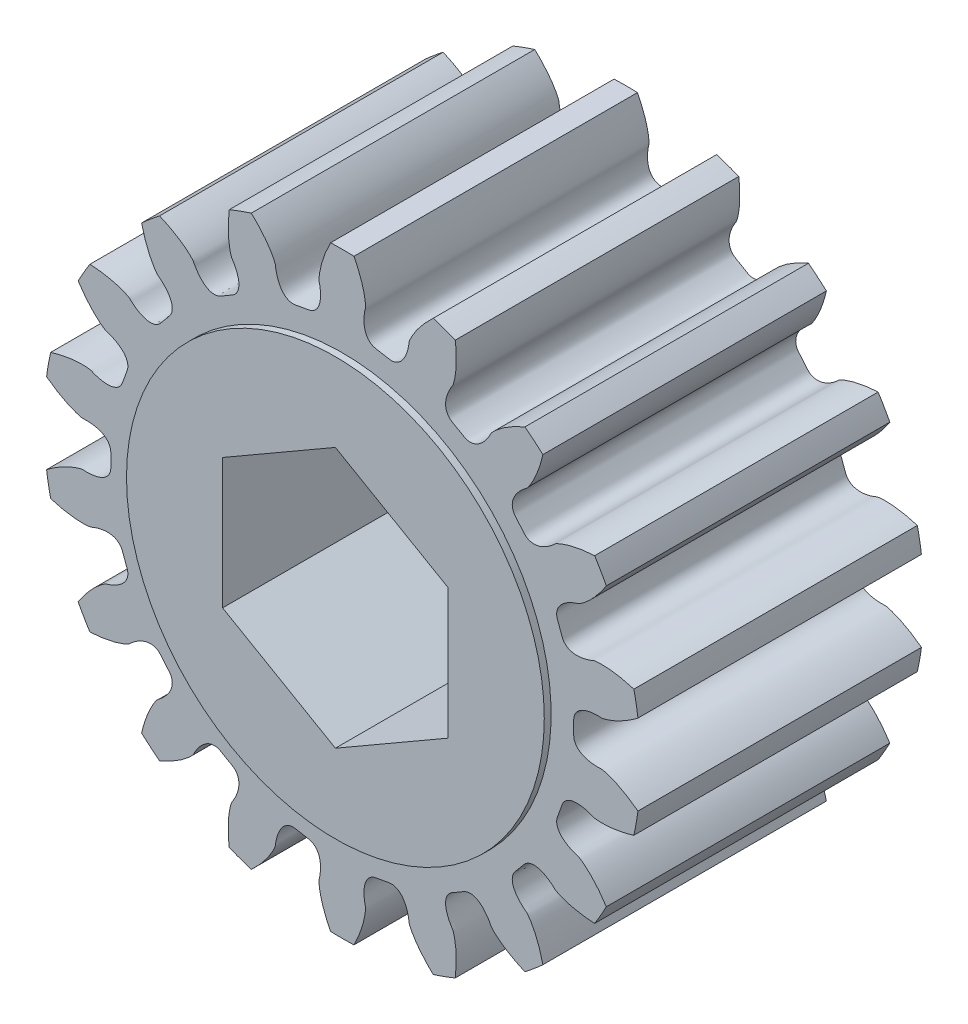
SolidWorks part; units mm, degrees
material "7075-T6 (SN)"
ref_plane "Front Plane" through (0, 0, 0) normal (0, 0, 1) x (1, 0, 0)
ref_plane "Top Plane" through (0, 0, 0) normal (0, 1, 0) x (1, 0, 0)
ref_plane "Right Plane" through (0, 0, 0) normal (1, 0, 0) x (0, 0, -1)
ref_plane "Plane1" through (0, 0, 6.0325) normal (0, 0, 1) x (1, 0, 0)
sketch "Sketch1" plane through (0, 0, 6.0325) normal (0, 0, 1) x (1, 0, 0)
  arc A0 (12.411, -2.694) -> (12.5839, -1.7132) centre (0, 0) ccw
  arc A1 (12.5839, 1.7132) -> (12.411, 2.694) centre (0, 0) ccw
  arc A2 (11.239, 5.9139) -> (10.7411, 6.7764) centre (0, 0) ccw
  arc A3 (8.5386, 9.4012) -> (7.7757, 10.0414) centre (0, 0) ccw
  arc A4 (4.8082, 11.7546) -> (3.8724, 12.0952) centre (0, 0) ccw
  arc A5 (0.498, 12.6902) -> (-0.498, 12.6902) centre (0, 0) ccw
  arc A6 (-3.8724, 12.0952) -> (-4.8082, 11.7546) centre (0, 0) ccw
  arc A7 (-7.7757, 10.0414) -> (-8.5386, 9.4012) centre (0, 0) ccw
  arc A8 (-10.7411, 6.7764) -> (-11.239, 5.9139) centre (0, 0) ccw
  arc A9 (-12.411, 2.694) -> (-12.5839, 1.7132) centre (0, 0) ccw
  arc A10 (-12.5839, -1.7132) -> (-12.411, -2.694) centre (0, 0) ccw
  arc A11 (-11.239, -5.9139) -> (-10.7411, -6.7764) centre (0, 0) ccw
  arc A12 (-8.5386, -9.4012) -> (-7.7757, -10.0414) centre (0, 0) ccw
  arc A13 (-4.8082, -11.7546) -> (-3.8724, -12.0952) centre (0, 0) ccw
  arc A14 (-0.498, -12.6902) -> (0.498, -12.6902) centre (0, 0) ccw
  arc A15 (3.8724, -12.0952) -> (4.8082, -11.7546) centre (0, 0) ccw
  arc A16 (7.7757, -10.0414) -> (8.5386, -9.4012) centre (0, 0) ccw
  arc A17 (10.7411, -6.7764) -> (11.239, -5.9139) centre (0, 0) ccw
  spline S0 degree 3 poles (11.239, -5.9139) (11.1509, -5.7775) (11.0298, -5.6051) (10.8706, -5.4047) (10.783, -5.3007) (10.6983, -5.2057) (10.6171, -5.1195) (10.5396, -5.0419) (10.4664, -4.9725) (10.3977, -4.911) (10.3341, -4.8571) (10.2759, -4.8106) (10.2233, -4.771) (10.1769, -4.7378) (10.1275, -4.7053) (10.0518, -4.6541) (9.95, -4.6355) (9.8549, -4.5968) (9.7835, -4.5675) (9.7159, -4.5362) (9.6517, -4.5038) (9.5908, -4.4699) (9.5333, -4.4347) (9.479, -4.3981) (9.4279, -4.3599) (9.3799, -4.3199) (9.3348, -4.2779) (9.2928, -4.2333) (9.2539, -4.1857) (9.2182, -4.1342) (9.1862, -4.078) (9.1588, -4.016) (9.1377, -3.9474) (9.125, -3.8716) (9.1237, -3.7895) (9.1359, -3.7108) (9.1798, -3.5695) (9.267, -3.3729) (9.3266, -3.1663) (9.3837, -3.0298) (9.425, -2.9616) (9.4787, -2.8996) (9.5372, -2.8497) (9.5975, -2.8107) (9.6583, -2.7808) (9.719, -2.7583) (9.7794, -2.7419) (9.8398, -2.7304) (9.9007, -2.7233) (9.9622, -2.72) (10.0247, -2.7203) (10.0884, -2.7238) (10.1535, -2.7307) (10.2202, -2.7407) (10.2886, -2.7539) (10.3586, -2.7703) (10.4305, -2.7899) (10.504, -2.8133) (10.6018, -2.8447) (10.6917, -2.8959) (10.7827, -2.9054) (10.8413, -2.9122) (10.8982, -2.9166) (10.9639, -2.9201) (11.0385, -2.9219) (11.1219, -2.9215) (11.2139, -2.9185) (11.3147, -2.9124) (11.4239, -2.9027) (11.5416, -2.889) (11.6675, -2.8706) (11.8014, -2.8472) (12.0522, -2.7961) (12.2559, -2.7418) (12.411, -2.694) knots 0 0 0 0 0.068568 0.088955 0.108106 0.126021 0.142701 0.158145 0.172354 0.185328 0.197065 0.207567 0.216834 0.224865 0.231661 0.241836 0.263156 0.274398 0.285253 0.295736 0.305862 0.315655 0.325139 0.334346 0.343315 0.352092 0.360737 0.369325 0.377945 0.38671 0.395752 0.405223 0.415278 0.426045 0.437578 0.449793 0.459544 0.5 0.540456 0.550207 0.562422 0.573955 0.584722 0.594777 0.604248 0.61329 0.622055 0.630675 0.639263 0.647908 0.656685 0.665654 0.674861 0.684345 0.694138 0.704264 0.714747 0.725602 0.736844 0.758164 0.768339 0.775135 0.783166 0.792433 0.802935 0.814672 0.827646 0.841855 0.857299 0.873979 0.891894 0.911045 0.931432 1 1 1 1
  spline S1 degree 3 poles (12.5839, -1.7132) (12.4545, -1.6153) (12.2817, -1.4946) (12.0635, -1.3608) (11.9456, -1.293) (11.8336, -1.2327) (11.7278, -1.1795) (11.6284, -1.133) (11.5359, -1.0929) (11.4503, -1.0586) (11.3721, -1.0297) (11.3015, -1.0059) (11.2385, -0.9867) (11.1836, -0.9714) (11.1261, -0.9577) (11.0374, -0.9355) (10.9354, -0.9529) (10.8328, -0.949) (10.7557, -0.9458) (10.6815, -0.9396) (10.61, -0.9311) (10.5412, -0.9201) (10.4751, -0.9067) (10.4116, -0.8909) (10.3505, -0.8724) (10.2917, -0.8513) (10.235, -0.8272) (10.1803, -0.7997) (10.1274, -0.7682) (10.0762, -0.7321) (10.027, -0.6902) (9.9801, -0.6413) (9.9367, -0.584) (9.8988, -0.5172) (9.8696, -0.4405) (9.8541, -0.3623) (9.847, -0.2145) (9.8618, 0) (9.847, 0.2145) (9.8541, 0.3623) (9.8696, 0.4405) (9.8988, 0.5172) (9.9367, 0.584) (9.9801, 0.6413) (10.027, 0.6902) (10.0762, 0.7321) (10.1274, 0.7682) (10.1803, 0.7997) (10.235, 0.8272) (10.2917, 0.8513) (10.3505, 0.8724) (10.4116, 0.8909) (10.4751, 0.9067) (10.5412, 0.9201) (10.61, 0.9311) (10.6815, 0.9396) (10.7557, 0.9458) (10.8328, 0.949) (10.9354, 0.9529) (11.0374, 0.9355) (11.1261, 0.9577) (11.1836, 0.9714) (11.2385, 0.9867) (11.3015, 1.0059) (11.3721, 1.0297) (11.4503, 1.0586) (11.5359, 1.0929) (11.6284, 1.133) (11.7278, 1.1795) (11.8336, 1.2327) (11.9456, 1.293) (12.0635, 1.3608) (12.2817, 1.4946) (12.4545, 1.6153) (12.5839, 1.7132) knots 0 0 0 0 0.068568 0.088955 0.108106 0.126021 0.142701 0.158145 0.172354 0.185328 0.197065 0.207567 0.216834 0.224865 0.231661 0.241836 0.263156 0.274398 0.285253 0.295736 0.305862 0.315655 0.325139 0.334346 0.343315 0.352092 0.360737 0.369325 0.377945 0.38671 0.395752 0.405223 0.415278 0.426045 0.437578 0.449793 0.459544 0.5 0.540456 0.550207 0.562422 0.573955 0.584722 0.594777 0.604248 0.61329 0.622055 0.630675 0.639263 0.647908 0.656685 0.665654 0.674861 0.684345 0.694138 0.704264 0.714747 0.725602 0.736844 0.758164 0.768339 0.775135 0.783166 0.792433 0.802935 0.814672 0.827646 0.841855 0.857299 0.873979 0.891894 0.911045 0.931432 1 1 1 1
  spline S2 degree 3 poles (12.411, 2.694) (12.2559, 2.7418) (12.0522, 2.7961) (11.8014, 2.8472) (11.6675, 2.8706) (11.5416, 2.889) (11.4239, 2.9027) (11.3147, 2.9124) (11.2139, 2.9185) (11.1219, 2.9215) (11.0385, 2.9219) (10.9639, 2.9201) (10.8982, 2.9166) (10.8413, 2.9122) (10.7827, 2.9054) (10.6917, 2.8959) (10.6018, 2.8447) (10.504, 2.8133) (10.4305, 2.7899) (10.3586, 2.7703) (10.2886, 2.7539) (10.2202, 2.7407) (10.1535, 2.7307) (10.0884, 2.7238) (10.0247, 2.7203) (9.9622, 2.72) (9.9007, 2.7233) (9.8398, 2.7304) (9.7794, 2.7419) (9.719, 2.7583) (9.6583, 2.7808) (9.5975, 2.8107) (9.5372, 2.8497) (9.4787, 2.8996) (9.425, 2.9616) (9.3837, 3.0298) (9.3266, 3.1663) (9.267, 3.3729) (9.1798, 3.5695) (9.1359, 3.7108) (9.1237, 3.7895) (9.125, 3.8716) (9.1377, 3.9474) (9.1588, 4.016) (9.1862, 4.078) (9.2182, 4.1342) (9.2539, 4.1857) (9.2928, 4.2333) (9.3348, 4.2779) (9.3799, 4.3199) (9.4279, 4.3599) (9.479, 4.3981) (9.5333, 4.4347) (9.5908, 4.4699) (9.6517, 4.5038) (9.7159, 4.5362) (9.7835, 4.5675) (9.8549, 4.5968) (9.95, 4.6355) (10.0518, 4.6541) (10.1275, 4.7053) (10.1769, 4.7378) (10.2233, 4.771) (10.2759, 4.8106) (10.3341, 4.8571) (10.3977, 4.911) (10.4664, 4.9725) (10.5396, 5.0419) (10.6171, 5.1195) (10.6983, 5.2057) (10.783, 5.3007) (10.8706, 5.4047) (11.0298, 5.6051) (11.1509, 5.7775) (11.239, 5.9139) knots 0 0 0 0 0.068568 0.088955 0.108106 0.126021 0.142701 0.158145 0.172354 0.185328 0.197065 0.207567 0.216834 0.224865 0.231661 0.241836 0.263156 0.274398 0.285253 0.295736 0.305862 0.315655 0.325139 0.334346 0.343315 0.352092 0.360737 0.369325 0.377945 0.38671 0.395752 0.405223 0.415278 0.426045 0.437578 0.449793 0.459544 0.5 0.540456 0.550207 0.562422 0.573955 0.584722 0.594777 0.604248 0.61329 0.622055 0.630675 0.639263 0.647908 0.656685 0.665654 0.674861 0.684345 0.694138 0.704264 0.714747 0.725602 0.736844 0.758164 0.768339 0.775135 0.783166 0.792433 0.802935 0.814672 0.827646 0.841855 0.857299 0.873979 0.891894 0.911045 0.931432 1 1 1 1
  spline S3 degree 3 poles (10.7411, 6.7764) (10.579, 6.7682) (10.369, 6.7496) (10.1159, 6.7118) (9.982, 6.688) (9.8574, 6.6622) (9.7422, 6.6349) (9.6362, 6.6066) (9.5395, 6.5779) (9.4519, 6.5492) (9.3735, 6.521) (9.304, 6.4939) (9.2434, 6.4682) (9.1915, 6.4445) (9.1387, 6.418) (9.0565, 6.3781) (8.9895, 6.2992) (8.9084, 6.2362) (8.8473, 6.1891) (8.7864, 6.1461) (8.7262, 6.1067) (8.6665, 6.0709) (8.6073, 6.0387) (8.5484, 6.01) (8.4897, 5.9848) (8.4311, 5.9632) (8.3722, 5.9453) (8.3126, 5.9312) (8.2518, 5.9212) (8.1894, 5.916) (8.1248, 5.9165) (8.0574, 5.9238) (7.9873, 5.9398) (7.9154, 5.9667) (7.8437, 6.0066) (7.7815, 6.0565) (7.6812, 6.1652) (7.5546, 6.339) (7.4054, 6.4939) (7.3157, 6.6116) (7.2774, 6.6815) (7.2505, 6.759) (7.2365, 6.8346) (7.2329, 6.9064) (7.2374, 6.974) (7.2483, 7.0377) (7.2642, 7.0983) (7.2845, 7.1563) (7.3088, 7.2126) (7.3367, 7.2675) (7.3681, 7.3215) (7.4031, 7.3749) (7.4416, 7.4279) (7.4836, 7.4806) (7.5292, 7.5332) (7.5785, 7.5857) (7.6314, 7.6382) (7.6884, 7.6901) (7.7645, 7.7591) (7.8538, 7.8113) (7.9074, 7.8854) (7.9427, 7.9328) (7.975, 7.9798) (8.0108, 8.035) (8.0497, 8.0987) (8.091, 8.1711) (8.1345, 8.2523) (8.1796, 8.3426) (8.2258, 8.442) (8.2727, 8.5508) (8.3198, 8.669) (8.3665, 8.7967) (8.4476, 9.0394) (8.5024, 9.243) (8.5386, 9.4012) knots 0 0 0 0 0.068568 0.088955 0.108106 0.126021 0.142701 0.158145 0.172354 0.185328 0.197065 0.207567 0.216834 0.224865 0.231661 0.241836 0.263156 0.274398 0.285253 0.295736 0.305862 0.315655 0.325139 0.334346 0.343315 0.352092 0.360737 0.369325 0.377945 0.38671 0.395752 0.405223 0.415278 0.426045 0.437578 0.449793 0.459544 0.5 0.540456 0.550207 0.562422 0.573955 0.584722 0.594777 0.604248 0.61329 0.622055 0.630675 0.639263 0.647908 0.656685 0.665654 0.674861 0.684345 0.694138 0.704264 0.714747 0.725602 0.736844 0.758164 0.768339 0.775135 0.783166 0.792433 0.802935 0.814672 0.827646 0.841855 0.857299 0.873979 0.891894 0.911045 0.931432 1 1 1 1
  spline S4 degree 3 poles (7.7757, 10.0414) (7.6261, 9.9783) (7.4352, 9.889) (7.2103, 9.7669) (7.0926, 9.6987) (6.9844, 9.6318) (6.8854, 9.5668) (6.7955, 9.504) (6.7144, 9.4439) (6.6419, 9.387) (6.5778, 9.3337) (6.5219, 9.2844) (6.4737, 9.2395) (6.433, 9.1996) (6.3925, 9.1566) (6.3289, 9.0909) (6.2929, 8.9939) (6.2382, 8.907) (6.197, 8.8418) (6.1544, 8.7806) (6.1113, 8.723) (6.0675, 8.6689) (6.0228, 8.6184) (5.9773, 8.5713) (5.9308, 8.5276) (5.8831, 8.4872) (5.8339, 8.4502) (5.7827, 8.4166) (5.729, 8.3865) (5.6721, 8.3602) (5.6112, 8.3385) (5.5455, 8.3223) (5.4741, 8.3134) (5.3973, 8.3141) (5.3163, 8.327) (5.2408, 8.3527) (5.1093, 8.4205) (4.9309, 8.5405) (4.7377, 8.6351) (4.6132, 8.715) (4.5533, 8.7675) (4.5016, 8.8312) (4.4626, 8.8974) (4.4346, 8.9637) (4.4157, 9.0287) (4.4041, 9.0923) (4.3984, 9.1547) (4.3976, 9.2162) (4.4012, 9.2774) (4.4086, 9.3385) (4.4197, 9.4) (4.4343, 9.4621) (4.4523, 9.5251) (4.4738, 9.589) (4.4987, 9.6541) (4.527, 9.7202) (4.5587, 9.7876) (4.5945, 9.8559) (4.6425, 9.9467) (4.7085, 10.0264) (4.7336, 10.1143) (4.7506, 10.1709) (4.7648, 10.2262) (4.7796, 10.2903) (4.7943, 10.3634) (4.8084, 10.4456) (4.8215, 10.5368) (4.833, 10.637) (4.8424, 10.7463) (4.8492, 10.8646) (4.853, 10.9917) (4.8533, 11.1277) (4.8465, 11.3836) (4.8284, 11.5935) (4.8082, 11.7546) knots 0 0 0 0 0.068568 0.088955 0.108106 0.126021 0.142701 0.158145 0.172354 0.185328 0.197065 0.207567 0.216834 0.224865 0.231661 0.241836 0.263156 0.274398 0.285253 0.295736 0.305862 0.315655 0.325139 0.334346 0.343315 0.352092 0.360737 0.369325 0.377945 0.38671 0.395752 0.405223 0.415278 0.426045 0.437578 0.449793 0.459544 0.5 0.540456 0.550207 0.562422 0.573955 0.584722 0.594777 0.604248 0.61329 0.622055 0.630675 0.639263 0.647908 0.656685 0.665654 0.674861 0.684345 0.694138 0.704264 0.714747 0.725602 0.736844 0.758164 0.768339 0.775135 0.783166 0.792433 0.802935 0.814672 0.827646 0.841855 0.857299 0.873979 0.891894 0.911045 0.931432 1 1 1 1
  spline S5 degree 3 poles (3.8724, 12.0952) (3.7534, 11.9848) (3.6046, 11.8356) (3.435, 11.644) (3.3477, 11.5396) (3.2689, 11.4398) (3.1981, 11.3448) (3.1351, 11.255) (3.0794, 11.1708) (3.0308, 11.0926) (2.9888, 11.0205) (2.9531, 10.9551) (2.9232, 10.8965) (2.8986, 10.845) (2.8752, 10.7907) (2.8379, 10.7073) (2.8373, 10.6038) (2.8157, 10.5034) (2.7992, 10.428) (2.7801, 10.356) (2.7593, 10.2871) (2.7366, 10.2213) (2.7119, 10.1586) (2.6853, 10.0987) (2.6565, 10.0418) (2.6255, 9.9875) (2.5919, 9.9359) (2.5553, 9.8868) (2.5152, 9.8401) (2.4707, 9.796) (2.4209, 9.7548) (2.3646, 9.7171) (2.3006, 9.6843) (2.2282, 9.6587) (2.1477, 9.6431) (2.068, 9.6414) (1.9212, 9.6602) (1.7125, 9.7119) (1.4986, 9.7347) (1.3543, 9.7673) (1.28, 9.7961) (1.2096, 9.8383) (1.1503, 9.8871) (1.1014, 9.9398) (1.0614, 9.9945) (1.0287, 10.0503) (1.002, 10.1069) (0.9803, 10.1645) (0.9627, 10.2231) (0.9488, 10.2832) (0.9382, 10.3447) (0.9306, 10.4081) (0.926, 10.4735) (0.9243, 10.5409) (0.9255, 10.6105) (0.9295, 10.6823) (0.9362, 10.7565) (0.9465, 10.833) (0.9605, 10.9347) (0.9953, 11.0321) (0.9888, 11.1233) (0.9854, 11.1823) (0.9799, 11.2391) (0.9719, 11.3044) (0.9607, 11.3782) (0.9458, 11.4602) (0.9269, 11.5504) (0.9034, 11.6485) (0.8749, 11.7544) (0.8409, 11.8679) (0.801, 11.9887) (0.7547, 12.1166) (0.6608, 12.3546) (0.572, 12.5458) (0.498, 12.6902) knots 0 0 0 0 0.068568 0.088955 0.108106 0.126021 0.142701 0.158145 0.172354 0.185328 0.197065 0.207567 0.216834 0.224865 0.231661 0.241836 0.263156 0.274398 0.285253 0.295736 0.305862 0.315655 0.325139 0.334346 0.343315 0.352092 0.360737 0.369325 0.377945 0.38671 0.395752 0.405223 0.415278 0.426045 0.437578 0.449793 0.459544 0.5 0.540456 0.550207 0.562422 0.573955 0.584722 0.594777 0.604248 0.61329 0.622055 0.630675 0.639263 0.647908 0.656685 0.665654 0.674861 0.684345 0.694138 0.704264 0.714747 0.725602 0.736844 0.758164 0.768339 0.775135 0.783166 0.792433 0.802935 0.814672 0.827646 0.841855 0.857299 0.873979 0.891894 0.911045 0.931432 1 1 1 1
  spline S6 degree 3 poles (-0.498, 12.6902) (-0.572, 12.5458) (-0.6608, 12.3546) (-0.7547, 12.1166) (-0.801, 11.9887) (-0.8409, 11.8679) (-0.8749, 11.7544) (-0.9034, 11.6485) (-0.9269, 11.5504) (-0.9458, 11.4602) (-0.9607, 11.3782) (-0.9719, 11.3044) (-0.9799, 11.2391) (-0.9854, 11.1823) (-0.9888, 11.1233) (-0.9953, 11.0321) (-0.9605, 10.9347) (-0.9465, 10.833) (-0.9362, 10.7565) (-0.9295, 10.6823) (-0.9255, 10.6105) (-0.9243, 10.5409) (-0.926, 10.4735) (-0.9306, 10.4081) (-0.9382, 10.3447) (-0.9488, 10.2832) (-0.9627, 10.2231) (-0.9803, 10.1645) (-1.002, 10.1069) (-1.0287, 10.0503) (-1.0614, 9.9945) (-1.1014, 9.9398) (-1.1503, 9.8871) (-1.2096, 9.8383) (-1.28, 9.7961) (-1.3543, 9.7673) (-1.4986, 9.7347) (-1.7125, 9.7119) (-1.9212, 9.6602) (-2.068, 9.6414) (-2.1477, 9.6431) (-2.2282, 9.6587) (-2.3006, 9.6843) (-2.3646, 9.7171) (-2.4209, 9.7548) (-2.4707, 9.796) (-2.5152, 9.8401) (-2.5553, 9.8868) (-2.5919, 9.9359) (-2.6255, 9.9875) (-2.6565, 10.0418) (-2.6853, 10.0987) (-2.7119, 10.1586) (-2.7366, 10.2213) (-2.7593, 10.2871) (-2.7801, 10.356) (-2.7992, 10.428) (-2.8157, 10.5034) (-2.8373, 10.6038) (-2.8379, 10.7073) (-2.8752, 10.7907) (-2.8986, 10.845) (-2.9232, 10.8965) (-2.9531, 10.9551) (-2.9888, 11.0205) (-3.0308, 11.0926) (-3.0794, 11.1708) (-3.1351, 11.255) (-3.1981, 11.3448) (-3.2689, 11.4398) (-3.3477, 11.5396) (-3.435, 11.644) (-3.6046, 11.8356) (-3.7534, 11.9848) (-3.8724, 12.0952) knots 0 0 0 0 0.068568 0.088955 0.108106 0.126021 0.142701 0.158145 0.172354 0.185328 0.197065 0.207567 0.216834 0.224865 0.231661 0.241836 0.263156 0.274398 0.285253 0.295736 0.305862 0.315655 0.325139 0.334346 0.343315 0.352092 0.360737 0.369325 0.377945 0.38671 0.395752 0.405223 0.415278 0.426045 0.437578 0.449793 0.459544 0.5 0.540456 0.550207 0.562422 0.573955 0.584722 0.594777 0.604248 0.61329 0.622055 0.630675 0.639263 0.647908 0.656685 0.665654 0.674861 0.684345 0.694138 0.704264 0.714747 0.725602 0.736844 0.758164 0.768339 0.775135 0.783166 0.792433 0.802935 0.814672 0.827646 0.841855 0.857299 0.873979 0.891894 0.911045 0.931432 1 1 1 1
  spline S7 degree 3 poles (-4.8082, 11.7546) (-4.8284, 11.5935) (-4.8465, 11.3836) (-4.8533, 11.1277) (-4.853, 10.9917) (-4.8492, 10.8646) (-4.8424, 10.7463) (-4.833, 10.637) (-4.8215, 10.5368) (-4.8084, 10.4456) (-4.7943, 10.3634) (-4.7796, 10.2903) (-4.7648, 10.2262) (-4.7506, 10.1709) (-4.7336, 10.1143) (-4.7085, 10.0264) (-4.6425, 9.9467) (-4.5945, 9.8559) (-4.5587, 9.7876) (-4.527, 9.7202) (-4.4987, 9.6541) (-4.4738, 9.589) (-4.4523, 9.5251) (-4.4343, 9.4621) (-4.4197, 9.4) (-4.4086, 9.3385) (-4.4012, 9.2774) (-4.3976, 9.2162) (-4.3984, 9.1547) (-4.4041, 9.0923) (-4.4157, 9.0287) (-4.4346, 8.9637) (-4.4626, 8.8974) (-4.5016, 8.8312) (-4.5533, 8.7675) (-4.6132, 8.715) (-4.7377, 8.6351) (-4.9309, 8.5405) (-5.1093, 8.4205) (-5.2408, 8.3527) (-5.3163, 8.327) (-5.3973, 8.3141) (-5.4741, 8.3134) (-5.5455, 8.3223) (-5.6112, 8.3385) (-5.6721, 8.3602) (-5.729, 8.3865) (-5.7827, 8.4166) (-5.8339, 8.4502) (-5.8831, 8.4872) (-5.9308, 8.5276) (-5.9773, 8.5713) (-6.0228, 8.6184) (-6.0675, 8.6689) (-6.1113, 8.723) (-6.1544, 8.7806) (-6.197, 8.8418) (-6.2382, 8.907) (-6.2929, 8.9939) (-6.3289, 9.0909) (-6.3925, 9.1566) (-6.433, 9.1996) (-6.4737, 9.2395) (-6.5219, 9.2844) (-6.5778, 9.3337) (-6.6419, 9.387) (-6.7144, 9.4439) (-6.7954, 9.504) (-6.8854, 9.5668) (-6.9844, 9.6318) (-7.0926, 9.6987) (-7.2103, 9.7669) (-7.4352, 9.889) (-7.6261, 9.9783) (-7.7757, 10.0414) knots 0 0 0 0 0.068568 0.088955 0.108106 0.126021 0.142701 0.158145 0.172354 0.185328 0.197065 0.207567 0.216834 0.224865 0.231661 0.241836 0.263156 0.274398 0.285253 0.295736 0.305862 0.315655 0.325139 0.334346 0.343315 0.352092 0.360737 0.369325 0.377945 0.38671 0.395752 0.405223 0.415278 0.426045 0.437578 0.449793 0.459544 0.5 0.540456 0.550207 0.562422 0.573955 0.584722 0.594777 0.604248 0.61329 0.622055 0.630675 0.639263 0.647908 0.656685 0.665654 0.674861 0.684345 0.694138 0.704264 0.714747 0.725602 0.736844 0.758164 0.768339 0.775135 0.783166 0.792433 0.802935 0.814672 0.827646 0.841855 0.857299 0.873979 0.891894 0.911045 0.931432 1 1 1 1
  spline S8 degree 3 poles (-8.5386, 9.4012) (-8.5024, 9.243) (-8.4476, 9.0394) (-8.3665, 8.7967) (-8.3198, 8.669) (-8.2727, 8.5508) (-8.2258, 8.442) (-8.1796, 8.3426) (-8.1345, 8.2523) (-8.091, 8.1711) (-8.0497, 8.0987) (-8.0108, 8.035) (-7.975, 7.9798) (-7.9427, 7.9328) (-7.9074, 7.8854) (-7.8538, 7.8113) (-7.7645, 7.7591) (-7.6884, 7.6901) (-7.6314, 7.6382) (-7.5785, 7.5857) (-7.5292, 7.5332) (-7.4836, 7.4806) (-7.4416, 7.4279) (-7.4031, 7.3749) (-7.3681, 7.3215) (-7.3367, 7.2675) (-7.3088, 7.2126) (-7.2845, 7.1563) (-7.2642, 7.0983) (-7.2483, 7.0377) (-7.2374, 6.974) (-7.2329, 6.9064) (-7.2365, 6.8346) (-7.2505, 6.759) (-7.2774, 6.6815) (-7.3157, 6.6116) (-7.4054, 6.4939) (-7.5546, 6.339) (-7.6812, 6.1652) (-7.7815, 6.0565) (-7.8437, 6.0066) (-7.9154, 5.9667) (-7.9873, 5.9398) (-8.0574, 5.9238) (-8.1248, 5.9165) (-8.1894, 5.916) (-8.2518, 5.9212) (-8.3126, 5.9312) (-8.3722, 5.9453) (-8.4311, 5.9632) (-8.4897, 5.9848) (-8.5484, 6.01) (-8.6073, 6.0387) (-8.6665, 6.0709) (-8.7262, 6.1067) (-8.7864, 6.1461) (-8.8473, 6.1891) (-8.9084, 6.2362) (-8.9895, 6.2992) (-9.0565, 6.3781) (-9.1387, 6.418) (-9.1915, 6.4445) (-9.2434, 6.4682) (-9.304, 6.4939) (-9.3735, 6.521) (-9.4519, 6.5492) (-9.5395, 6.5779) (-9.6362, 6.6066) (-9.7422, 6.6349) (-9.8574, 6.6622) (-9.982, 6.688) (-10.1159, 6.7118) (-10.369, 6.7496) (-10.579, 6.7682) (-10.7411, 6.7764) knots 0 0 0 0 0.068568 0.088955 0.108106 0.126021 0.142701 0.158145 0.172354 0.185328 0.197065 0.207567 0.216834 0.224865 0.231661 0.241836 0.263156 0.274398 0.285253 0.295736 0.305862 0.315655 0.325139 0.334346 0.343315 0.352092 0.360737 0.369325 0.377945 0.38671 0.395752 0.405223 0.415278 0.426045 0.437578 0.449793 0.459544 0.5 0.540456 0.550207 0.562422 0.573955 0.584722 0.594777 0.604248 0.61329 0.622055 0.630675 0.639263 0.647908 0.656685 0.665654 0.674861 0.684345 0.694138 0.704264 0.714747 0.725602 0.736844 0.758164 0.768339 0.775135 0.783166 0.792433 0.802935 0.814672 0.827646 0.841855 0.857299 0.873979 0.891894 0.911045 0.931432 1 1 1 1
  spline S9 degree 3 poles (-11.239, 5.9139) (-11.1509, 5.7775) (-11.0298, 5.6051) (-10.8706, 5.4047) (-10.783, 5.3007) (-10.6983, 5.2057) (-10.6171, 5.1195) (-10.5396, 5.0419) (-10.4664, 4.9725) (-10.3977, 4.911) (-10.3341, 4.8571) (-10.2759, 4.8106) (-10.2233, 4.771) (-10.1769, 4.7378) (-10.1275, 4.7053) (-10.0518, 4.6541) (-9.95, 4.6355) (-9.8549, 4.5968) (-9.7835, 4.5675) (-9.7159, 4.5362) (-9.6517, 4.5038) (-9.5908, 4.4699) (-9.5333, 4.4347) (-9.479, 4.3981) (-9.4279, 4.3599) (-9.3799, 4.3199) (-9.3348, 4.2779) (-9.2928, 4.2333) (-9.2539, 4.1857) (-9.2182, 4.1342) (-9.1862, 4.078) (-9.1588, 4.016) (-9.1377, 3.9474) (-9.125, 3.8716) (-9.1237, 3.7895) (-9.1359, 3.7108) (-9.1798, 3.5695) (-9.267, 3.3729) (-9.3266, 3.1663) (-9.3837, 3.0298) (-9.425, 2.9616) (-9.4787, 2.8996) (-9.5372, 2.8497) (-9.5975, 2.8107) (-9.6583, 2.7808) (-9.719, 2.7583) (-9.7794, 2.7419) (-9.8398, 2.7304) (-9.9007, 2.7233) (-9.9622, 2.72) (-10.0247, 2.7203) (-10.0884, 2.7238) (-10.1535, 2.7307) (-10.2202, 2.7407) (-10.2886, 2.7539) (-10.3586, 2.7703) (-10.4305, 2.7899) (-10.504, 2.8133) (-10.6018, 2.8447) (-10.6917, 2.8959) (-10.7827, 2.9054) (-10.8413, 2.9122) (-10.8982, 2.9166) (-10.9639, 2.9201) (-11.0385, 2.9219) (-11.1219, 2.9215) (-11.2139, 2.9185) (-11.3147, 2.9124) (-11.4239, 2.9027) (-11.5416, 2.889) (-11.6675, 2.8706) (-11.8014, 2.8472) (-12.0522, 2.7961) (-12.2559, 2.7418) (-12.411, 2.694) knots 0 0 0 0 0.068568 0.088955 0.108106 0.126021 0.142701 0.158145 0.172354 0.185328 0.197065 0.207567 0.216834 0.224865 0.231661 0.241836 0.263156 0.274398 0.285253 0.295736 0.305862 0.315655 0.325139 0.334346 0.343315 0.352092 0.360737 0.369325 0.377945 0.38671 0.395752 0.405223 0.415278 0.426045 0.437578 0.449793 0.459544 0.5 0.540456 0.550207 0.562422 0.573955 0.584722 0.594777 0.604248 0.61329 0.622055 0.630675 0.639263 0.647908 0.656685 0.665654 0.674861 0.684345 0.694138 0.704264 0.714747 0.725602 0.736844 0.758164 0.768339 0.775135 0.783166 0.792433 0.802935 0.814672 0.827646 0.841855 0.857299 0.873979 0.891894 0.911045 0.931432 1 1 1 1
  spline S10 degree 3 poles (-12.5839, 1.7132) (-12.4545, 1.6153) (-12.2817, 1.4946) (-12.0635, 1.3608) (-11.9456, 1.293) (-11.8336, 1.2327) (-11.7278, 1.1795) (-11.6284, 1.133) (-11.5359, 1.0929) (-11.4503, 1.0586) (-11.3721, 1.0297) (-11.3015, 1.0059) (-11.2385, 0.9867) (-11.1836, 0.9714) (-11.1261, 0.9577) (-11.0374, 0.9355) (-10.9354, 0.9529) (-10.8328, 0.949) (-10.7557, 0.9458) (-10.6815, 0.9396) (-10.61, 0.9311) (-10.5412, 0.9201) (-10.4751, 0.9067) (-10.4116, 0.8909) (-10.3505, 0.8724) (-10.2917, 0.8513) (-10.235, 0.8272) (-10.1803, 0.7997) (-10.1274, 0.7682) (-10.0762, 0.7321) (-10.027, 0.6902) (-9.9801, 0.6413) (-9.9367, 0.584) (-9.8988, 0.5172) (-9.8696, 0.4405) (-9.8541, 0.3623) (-9.847, 0.2145) (-9.8618, 0) (-9.847, -0.2145) (-9.8541, -0.3623) (-9.8696, -0.4405) (-9.8988, -0.5172) (-9.9367, -0.584) (-9.9801, -0.6413) (-10.027, -0.6902) (-10.0762, -0.7321) (-10.1274, -0.7682) (-10.1803, -0.7997) (-10.235, -0.8272) (-10.2917, -0.8513) (-10.3505, -0.8724) (-10.4116, -0.8909) (-10.4751, -0.9067) (-10.5412, -0.9201) (-10.61, -0.9311) (-10.6815, -0.9396) (-10.7557, -0.9458) (-10.8328, -0.949) (-10.9354, -0.9529) (-11.0374, -0.9355) (-11.1261, -0.9577) (-11.1836, -0.9714) (-11.2385, -0.9867) (-11.3015, -1.0059) (-11.3721, -1.0297) (-11.4503, -1.0586) (-11.5359, -1.0929) (-11.6284, -1.133) (-11.7278, -1.1795) (-11.8336, -1.2327) (-11.9456, -1.293) (-12.0635, -1.3608) (-12.2817, -1.4946) (-12.4545, -1.6153) (-12.5839, -1.7132) knots 0 0 0 0 0.068568 0.088955 0.108106 0.126021 0.142701 0.158145 0.172354 0.185328 0.197065 0.207567 0.216834 0.224865 0.231661 0.241836 0.263156 0.274398 0.285253 0.295736 0.305862 0.315655 0.325139 0.334346 0.343315 0.352092 0.360737 0.369325 0.377945 0.38671 0.395752 0.405223 0.415278 0.426045 0.437578 0.449793 0.459544 0.5 0.540456 0.550207 0.562422 0.573955 0.584722 0.594777 0.604248 0.61329 0.622055 0.630675 0.639263 0.647908 0.656685 0.665654 0.674861 0.684345 0.694138 0.704264 0.714747 0.725602 0.736844 0.758164 0.768339 0.775135 0.783166 0.792433 0.802935 0.814672 0.827646 0.841855 0.857299 0.873979 0.891894 0.911045 0.931432 1 1 1 1
  spline S11 degree 3 poles (-12.411, -2.694) (-12.2559, -2.7418) (-12.0522, -2.7961) (-11.8014, -2.8472) (-11.6675, -2.8706) (-11.5416, -2.889) (-11.4239, -2.9027) (-11.3147, -2.9124) (-11.2139, -2.9185) (-11.1219, -2.9215) (-11.0385, -2.9219) (-10.9639, -2.9201) (-10.8982, -2.9166) (-10.8413, -2.9122) (-10.7827, -2.9054) (-10.6917, -2.8959) (-10.6018, -2.8447) (-10.504, -2.8133) (-10.4305, -2.7899) (-10.3586, -2.7703) (-10.2886, -2.7539) (-10.2202, -2.7407) (-10.1535, -2.7307) (-10.0884, -2.7238) (-10.0247, -2.7203) (-9.9622, -2.72) (-9.9007, -2.7233) (-9.8398, -2.7304) (-9.7794, -2.7419) (-9.719, -2.7583) (-9.6583, -2.7808) (-9.5975, -2.8107) (-9.5372, -2.8497) (-9.4787, -2.8996) (-9.425, -2.9616) (-9.3837, -3.0298) (-9.3266, -3.1663) (-9.267, -3.3729) (-9.1798, -3.5695) (-9.1359, -3.7108) (-9.1237, -3.7895) (-9.125, -3.8716) (-9.1377, -3.9474) (-9.1588, -4.016) (-9.1862, -4.078) (-9.2182, -4.1342) (-9.2539, -4.1857) (-9.2928, -4.2333) (-9.3348, -4.2779) (-9.3799, -4.3199) (-9.4279, -4.3599) (-9.479, -4.3981) (-9.5333, -4.4347) (-9.5908, -4.4699) (-9.6517, -4.5038) (-9.7159, -4.5362) (-9.7835, -4.5675) (-9.8549, -4.5968) (-9.95, -4.6355) (-10.0518, -4.6541) (-10.1275, -4.7053) (-10.1769, -4.7378) (-10.2233, -4.771) (-10.2759, -4.8106) (-10.3341, -4.8571) (-10.3977, -4.911) (-10.4664, -4.9725) (-10.5396, -5.0419) (-10.6171, -5.1195) (-10.6983, -5.2057) (-10.783, -5.3007) (-10.8706, -5.4047) (-11.0298, -5.6051) (-11.1509, -5.7775) (-11.239, -5.9139) knots 0 0 0 0 0.068568 0.088955 0.108106 0.126021 0.142701 0.158145 0.172354 0.185328 0.197065 0.207567 0.216834 0.224865 0.231661 0.241836 0.263156 0.274398 0.285253 0.295736 0.305862 0.315655 0.325139 0.334346 0.343315 0.352092 0.360737 0.369325 0.377945 0.38671 0.395752 0.405223 0.415278 0.426045 0.437578 0.449793 0.459544 0.5 0.540456 0.550207 0.562422 0.573955 0.584722 0.594777 0.604248 0.61329 0.622055 0.630675 0.639263 0.647908 0.656685 0.665654 0.674861 0.684345 0.694138 0.704264 0.714747 0.725602 0.736844 0.758164 0.768339 0.775135 0.783166 0.792433 0.802935 0.814672 0.827646 0.841855 0.857299 0.873979 0.891894 0.911045 0.931432 1 1 1 1
  spline S12 degree 3 poles (-10.7411, -6.7764) (-10.579, -6.7682) (-10.369, -6.7496) (-10.1159, -6.7118) (-9.982, -6.688) (-9.8574, -6.6622) (-9.7422, -6.6349) (-9.6362, -6.6066) (-9.5395, -6.5779) (-9.4519, -6.5492) (-9.3735, -6.521) (-9.304, -6.4939) (-9.2434, -6.4682) (-9.1915, -6.4445) (-9.1387, -6.418) (-9.0565, -6.3781) (-8.9895, -6.2992) (-8.9084, -6.2362) (-8.8473, -6.1891) (-8.7864, -6.1461) (-8.7262, -6.1067) (-8.6665, -6.0709) (-8.6073, -6.0387) (-8.5484, -6.01) (-8.4897, -5.9848) (-8.4311, -5.9632) (-8.3722, -5.9453) (-8.3126, -5.9312) (-8.2518, -5.9212) (-8.1894, -5.916) (-8.1248, -5.9165) (-8.0574, -5.9238) (-7.9873, -5.9398) (-7.9154, -5.9667) (-7.8437, -6.0066) (-7.7815, -6.0565) (-7.6812, -6.1652) (-7.5546, -6.339) (-7.4054, -6.4939) (-7.3157, -6.6116) (-7.2774, -6.6815) (-7.2505, -6.759) (-7.2365, -6.8346) (-7.2329, -6.9064) (-7.2374, -6.974) (-7.2483, -7.0377) (-7.2642, -7.0983) (-7.2845, -7.1563) (-7.3088, -7.2126) (-7.3367, -7.2675) (-7.3681, -7.3215) (-7.4031, -7.3749) (-7.4416, -7.4279) (-7.4836, -7.4806) (-7.5292, -7.5332) (-7.5785, -7.5857) (-7.6314, -7.6382) (-7.6884, -7.6901) (-7.7645, -7.7591) (-7.8538, -7.8113) (-7.9074, -7.8854) (-7.9427, -7.9328) (-7.975, -7.9798) (-8.0108, -8.035) (-8.0497, -8.0987) (-8.091, -8.1711) (-8.1345, -8.2523) (-8.1796, -8.3426) (-8.2258, -8.442) (-8.2727, -8.5508) (-8.3198, -8.669) (-8.3665, -8.7967) (-8.4476, -9.0394) (-8.5024, -9.243) (-8.5386, -9.4012) knots 0 0 0 0 0.068568 0.088955 0.108106 0.126021 0.142701 0.158145 0.172354 0.185328 0.197065 0.207567 0.216834 0.224865 0.231661 0.241836 0.263156 0.274398 0.285253 0.295736 0.305862 0.315655 0.325139 0.334346 0.343315 0.352092 0.360737 0.369325 0.377945 0.38671 0.395752 0.405223 0.415278 0.426045 0.437578 0.449793 0.459544 0.5 0.540456 0.550207 0.562422 0.573955 0.584722 0.594777 0.604248 0.61329 0.622055 0.630675 0.639263 0.647908 0.656685 0.665654 0.674861 0.684345 0.694138 0.704264 0.714747 0.725602 0.736844 0.758164 0.768339 0.775135 0.783166 0.792433 0.802935 0.814672 0.827646 0.841855 0.857299 0.873979 0.891894 0.911045 0.931432 1 1 1 1
  spline S13 degree 3 poles (-7.7757, -10.0414) (-7.6261, -9.9783) (-7.4352, -9.889) (-7.2103, -9.7669) (-7.0926, -9.6987) (-6.9844, -9.6318) (-6.8854, -9.5668) (-6.7954, -9.504) (-6.7144, -9.4439) (-6.6419, -9.387) (-6.5778, -9.3337) (-6.5219, -9.2844) (-6.4737, -9.2395) (-6.433, -9.1996) (-6.3925, -9.1566) (-6.3289, -9.0909) (-6.2929, -8.9939) (-6.2382, -8.907) (-6.197, -8.8418) (-6.1544, -8.7806) (-6.1113, -8.723) (-6.0675, -8.6689) (-6.0228, -8.6184) (-5.9773, -8.5713) (-5.9308, -8.5276) (-5.8831, -8.4872) (-5.8339, -8.4502) (-5.7827, -8.4166) (-5.729, -8.3865) (-5.6721, -8.3602) (-5.6112, -8.3385) (-5.5455, -8.3223) (-5.4741, -8.3134) (-5.3973, -8.3141) (-5.3163, -8.327) (-5.2408, -8.3527) (-5.1093, -8.4205) (-4.9309, -8.5405) (-4.7377, -8.6351) (-4.6132, -8.715) (-4.5533, -8.7675) (-4.5016, -8.8312) (-4.4626, -8.8974) (-4.4346, -8.9637) (-4.4157, -9.0287) (-4.4041, -9.0923) (-4.3984, -9.1547) (-4.3976, -9.2162) (-4.4012, -9.2774) (-4.4086, -9.3385) (-4.4197, -9.4) (-4.4343, -9.4621) (-4.4523, -9.5251) (-4.4738, -9.589) (-4.4987, -9.6541) (-4.527, -9.7202) (-4.5587, -9.7876) (-4.5945, -9.8559) (-4.6425, -9.9467) (-4.7085, -10.0264) (-4.7336, -10.1143) (-4.7506, -10.1709) (-4.7648, -10.2262) (-4.7796, -10.2903) (-4.7943, -10.3634) (-4.8084, -10.4456) (-4.8215, -10.5368) (-4.833, -10.637) (-4.8424, -10.7463) (-4.8492, -10.8646) (-4.853, -10.9917) (-4.8533, -11.1277) (-4.8465, -11.3836) (-4.8284, -11.5935) (-4.8082, -11.7546) knots 0 0 0 0 0.068568 0.088955 0.108106 0.126021 0.142701 0.158145 0.172354 0.185328 0.197065 0.207567 0.216834 0.224865 0.231661 0.241836 0.263156 0.274398 0.285253 0.295736 0.305862 0.315655 0.325139 0.334346 0.343315 0.352092 0.360737 0.369325 0.377945 0.38671 0.395752 0.405223 0.415278 0.426045 0.437578 0.449793 0.459544 0.5 0.540456 0.550207 0.562422 0.573955 0.584722 0.594777 0.604248 0.61329 0.622055 0.630675 0.639263 0.647908 0.656685 0.665654 0.674861 0.684345 0.694138 0.704264 0.714747 0.725602 0.736844 0.758164 0.768339 0.775135 0.783166 0.792433 0.802935 0.814672 0.827646 0.841855 0.857299 0.873979 0.891894 0.911045 0.931432 1 1 1 1
  spline S14 degree 3 poles (-3.8724, -12.0952) (-3.7534, -11.9848) (-3.6046, -11.8356) (-3.435, -11.644) (-3.3477, -11.5396) (-3.2689, -11.4398) (-3.1981, -11.3448) (-3.1351, -11.255) (-3.0794, -11.1708) (-3.0308, -11.0926) (-2.9888, -11.0205) (-2.9531, -10.9551) (-2.9232, -10.8965) (-2.8986, -10.845) (-2.8752, -10.7907) (-2.8379, -10.7073) (-2.8373, -10.6038) (-2.8157, -10.5034) (-2.7992, -10.428) (-2.7801, -10.356) (-2.7593, -10.2871) (-2.7366, -10.2213) (-2.7119, -10.1586) (-2.6853, -10.0987) (-2.6565, -10.0418) (-2.6255, -9.9875) (-2.5919, -9.9359) (-2.5553, -9.8868) (-2.5152, -9.8401) (-2.4707, -9.796) (-2.4209, -9.7548) (-2.3646, -9.7171) (-2.3006, -9.6843) (-2.2282, -9.6587) (-2.1477, -9.6431) (-2.068, -9.6414) (-1.9212, -9.6602) (-1.7125, -9.7119) (-1.4986, -9.7347) (-1.3543, -9.7673) (-1.28, -9.7961) (-1.2096, -9.8383) (-1.1503, -9.8871) (-1.1014, -9.9398) (-1.0614, -9.9945) (-1.0287, -10.0503) (-1.002, -10.1069) (-0.9803, -10.1645) (-0.9627, -10.2231) (-0.9488, -10.2832) (-0.9382, -10.3447) (-0.9306, -10.4081) (-0.926, -10.4735) (-0.9243, -10.5409) (-0.9255, -10.6105) (-0.9295, -10.6823) (-0.9362, -10.7565) (-0.9465, -10.833) (-0.9605, -10.9347) (-0.9953, -11.0321) (-0.9888, -11.1233) (-0.9854, -11.1823) (-0.9799, -11.2391) (-0.9719, -11.3044) (-0.9607, -11.3782) (-0.9458, -11.4602) (-0.9269, -11.5504) (-0.9034, -11.6485) (-0.8749, -11.7544) (-0.8409, -11.8679) (-0.801, -11.9887) (-0.7547, -12.1166) (-0.6608, -12.3546) (-0.572, -12.5458) (-0.498, -12.6902) knots 0 0 0 0 0.068568 0.088955 0.108106 0.126021 0.142701 0.158145 0.172354 0.185328 0.197065 0.207567 0.216834 0.224865 0.231661 0.241836 0.263156 0.274398 0.285253 0.295736 0.305862 0.315655 0.325139 0.334346 0.343315 0.352092 0.360737 0.369325 0.377945 0.38671 0.395752 0.405223 0.415278 0.426045 0.437578 0.449793 0.459544 0.5 0.540456 0.550207 0.562422 0.573955 0.584722 0.594777 0.604248 0.61329 0.622055 0.630675 0.639263 0.647908 0.656685 0.665654 0.674861 0.684345 0.694138 0.704264 0.714747 0.725602 0.736844 0.758164 0.768339 0.775135 0.783166 0.792433 0.802935 0.814672 0.827646 0.841855 0.857299 0.873979 0.891894 0.911045 0.931432 1 1 1 1
  spline S15 degree 3 poles (0.498, -12.6902) (0.572, -12.5458) (0.6608, -12.3546) (0.7547, -12.1166) (0.801, -11.9887) (0.8409, -11.8679) (0.8749, -11.7544) (0.9034, -11.6485) (0.9269, -11.5504) (0.9458, -11.4602) (0.9607, -11.3782) (0.9719, -11.3044) (0.9799, -11.2391) (0.9854, -11.1823) (0.9888, -11.1233) (0.9953, -11.0321) (0.9605, -10.9347) (0.9465, -10.833) (0.9362, -10.7565) (0.9295, -10.6823) (0.9255, -10.6105) (0.9243, -10.5409) (0.926, -10.4735) (0.9306, -10.4081) (0.9382, -10.3447) (0.9488, -10.2832) (0.9627, -10.2231) (0.9803, -10.1645) (1.002, -10.1069) (1.0287, -10.0503) (1.0614, -9.9945) (1.1014, -9.9398) (1.1503, -9.8871) (1.2096, -9.8383) (1.28, -9.7961) (1.3543, -9.7673) (1.4986, -9.7347) (1.7125, -9.7119) (1.9212, -9.6602) (2.068, -9.6414) (2.1477, -9.6431) (2.2282, -9.6587) (2.3006, -9.6843) (2.3646, -9.7171) (2.4209, -9.7548) (2.4707, -9.796) (2.5152, -9.8401) (2.5553, -9.8868) (2.5919, -9.9359) (2.6255, -9.9875) (2.6565, -10.0418) (2.6853, -10.0987) (2.7119, -10.1586) (2.7366, -10.2213) (2.7593, -10.2871) (2.7801, -10.356) (2.7992, -10.428) (2.8157, -10.5034) (2.8373, -10.6038) (2.8379, -10.7073) (2.8752, -10.7907) (2.8986, -10.845) (2.9232, -10.8965) (2.9531, -10.9551) (2.9888, -11.0205) (3.0308, -11.0926) (3.0794, -11.1708) (3.1351, -11.255) (3.1981, -11.3448) (3.2689, -11.4398) (3.3477, -11.5396) (3.435, -11.644) (3.6046, -11.8356) (3.7534, -11.9848) (3.8724, -12.0952) knots 0 0 0 0 0.068568 0.088955 0.108106 0.126021 0.142701 0.158145 0.172354 0.185328 0.197065 0.207567 0.216834 0.224865 0.231661 0.241836 0.263156 0.274398 0.285253 0.295736 0.305862 0.315655 0.325139 0.334346 0.343315 0.352092 0.360737 0.369325 0.377945 0.38671 0.395752 0.405223 0.415278 0.426045 0.437578 0.449793 0.459544 0.5 0.540456 0.550207 0.562422 0.573955 0.584722 0.594777 0.604248 0.61329 0.622055 0.630675 0.639263 0.647908 0.656685 0.665654 0.674861 0.684345 0.694138 0.704264 0.714747 0.725602 0.736844 0.758164 0.768339 0.775135 0.783166 0.792433 0.802935 0.814672 0.827646 0.841855 0.857299 0.873979 0.891894 0.911045 0.931432 1 1 1 1
  spline S16 degree 3 poles (4.8082, -11.7546) (4.8284, -11.5935) (4.8465, -11.3836) (4.8533, -11.1277) (4.853, -10.9917) (4.8492, -10.8646) (4.8424, -10.7463) (4.833, -10.637) (4.8215, -10.5368) (4.8084, -10.4456) (4.7943, -10.3634) (4.7796, -10.2903) (4.7648, -10.2262) (4.7506, -10.1709) (4.7336, -10.1143) (4.7085, -10.0264) (4.6425, -9.9467) (4.5945, -9.8559) (4.5587, -9.7876) (4.527, -9.7202) (4.4987, -9.6541) (4.4738, -9.589) (4.4523, -9.5251) (4.4343, -9.4621) (4.4197, -9.4) (4.4086, -9.3385) (4.4012, -9.2774) (4.3976, -9.2162) (4.3984, -9.1547) (4.4041, -9.0923) (4.4157, -9.0287) (4.4346, -8.9637) (4.4626, -8.8974) (4.5016, -8.8312) (4.5533, -8.7675) (4.6132, -8.715) (4.7377, -8.6351) (4.9309, -8.5405) (5.1093, -8.4205) (5.2408, -8.3527) (5.3163, -8.327) (5.3973, -8.3141) (5.4741, -8.3134) (5.5455, -8.3223) (5.6112, -8.3385) (5.6721, -8.3602) (5.729, -8.3865) (5.7827, -8.4166) (5.8339, -8.4502) (5.8831, -8.4872) (5.9308, -8.5276) (5.9773, -8.5713) (6.0228, -8.6184) (6.0675, -8.6689) (6.1113, -8.723) (6.1544, -8.7806) (6.197, -8.8418) (6.2382, -8.907) (6.2929, -8.9939) (6.3289, -9.0909) (6.3925, -9.1566) (6.433, -9.1996) (6.4737, -9.2395) (6.5219, -9.2844) (6.5778, -9.3337) (6.6419, -9.387) (6.7144, -9.4439) (6.7955, -9.504) (6.8854, -9.5668) (6.9844, -9.6318) (7.0926, -9.6987) (7.2103, -9.7669) (7.4352, -9.889) (7.6261, -9.9783) (7.7757, -10.0414) knots 0 0 0 0 0.068568 0.088955 0.108106 0.126021 0.142701 0.158145 0.172354 0.185328 0.197065 0.207567 0.216834 0.224865 0.231661 0.241836 0.263156 0.274398 0.285253 0.295736 0.305862 0.315655 0.325139 0.334346 0.343315 0.352092 0.360737 0.369325 0.377945 0.38671 0.395752 0.405223 0.415278 0.426045 0.437578 0.449793 0.459544 0.5 0.540456 0.550207 0.562422 0.573955 0.584722 0.594777 0.604248 0.61329 0.622055 0.630675 0.639263 0.647908 0.656685 0.665654 0.674861 0.684345 0.694138 0.704264 0.714747 0.725602 0.736844 0.758164 0.768339 0.775135 0.783166 0.792433 0.802935 0.814672 0.827646 0.841855 0.857299 0.873979 0.891894 0.911045 0.931432 1 1 1 1
  spline S17 degree 3 poles (8.5386, -9.4012) (8.5024, -9.243) (8.4476, -9.0394) (8.3665, -8.7967) (8.3198, -8.669) (8.2727, -8.5508) (8.2258, -8.442) (8.1796, -8.3426) (8.1345, -8.2523) (8.091, -8.1711) (8.0497, -8.0987) (8.0108, -8.035) (7.975, -7.9798) (7.9427, -7.9328) (7.9074, -7.8854) (7.8538, -7.8113) (7.7645, -7.7591) (7.6884, -7.6901) (7.6314, -7.6382) (7.5785, -7.5857) (7.5292, -7.5332) (7.4836, -7.4806) (7.4416, -7.4279) (7.4031, -7.3749) (7.3681, -7.3215) (7.3367, -7.2675) (7.3088, -7.2126) (7.2845, -7.1563) (7.2642, -7.0983) (7.2483, -7.0377) (7.2374, -6.974) (7.2329, -6.9064) (7.2365, -6.8346) (7.2505, -6.759) (7.2774, -6.6815) (7.3157, -6.6116) (7.4054, -6.4939) (7.5546, -6.339) (7.6812, -6.1652) (7.7815, -6.0565) (7.8437, -6.0066) (7.9154, -5.9667) (7.9873, -5.9398) (8.0574, -5.9238) (8.1248, -5.9165) (8.1894, -5.916) (8.2518, -5.9212) (8.3126, -5.9312) (8.3722, -5.9453) (8.4311, -5.9632) (8.4897, -5.9848) (8.5484, -6.01) (8.6073, -6.0387) (8.6665, -6.0709) (8.7262, -6.1067) (8.7864, -6.1461) (8.8473, -6.1891) (8.9084, -6.2362) (8.9895, -6.2992) (9.0565, -6.3781) (9.1387, -6.418) (9.1915, -6.4445) (9.2434, -6.4682) (9.304, -6.4939) (9.3735, -6.521) (9.4519, -6.5492) (9.5395, -6.5779) (9.6362, -6.6066) (9.7422, -6.6349) (9.8574, -6.6622) (9.982, -6.688) (10.1159, -6.7118) (10.369, -6.7496) (10.579, -6.7682) (10.7411, -6.7764) knots 0 0 0 0 0.068568 0.088955 0.108106 0.126021 0.142701 0.158145 0.172354 0.185328 0.197065 0.207567 0.216834 0.224865 0.231661 0.241836 0.263156 0.274398 0.285253 0.295736 0.305862 0.315655 0.325139 0.334346 0.343315 0.352092 0.360737 0.369325 0.377945 0.38671 0.395752 0.405223 0.415278 0.426045 0.437578 0.449793 0.459544 0.5 0.540456 0.550207 0.562422 0.573955 0.584722 0.594777 0.604248 0.61329 0.622055 0.630675 0.639263 0.647908 0.656685 0.665654 0.674861 0.684345 0.694138 0.704264 0.714747 0.725602 0.736844 0.758164 0.768339 0.775135 0.783166 0.792433 0.802935 0.814672 0.827646 0.841855 0.857299 0.873979 0.891894 0.911045 0.931432 1 1 1 1
extrude "Boss-Extrude1" add sketch "Sketch1" against normal blind 12.065
sketch "Sketch2" plane through (0, 0, 6.0325) normal (0, 0, 1) x (1, 0, 0)
  circle A0 centre (0, 0) radius 8.89
extrude "Boss-Extrude2" add sketch "Sketch2" along normal blind 0.2921
sketch "Sketch3" plane through (0, 0, -6.0325) normal (0, 0, -1) x (-1, 0, 0)
  circle A0 centre (0, 0) radius 8.89
extrude "Boss-Extrude3" add sketch "Sketch3" along normal blind 0.2921
sketch "Sketch4" plane through (0, 0, -6.3246) normal (0, 0, -1) x (-1, 0, 0)
  line L0 (0, -5.5433) -> (4.8006, -2.7716)
  line L1 (4.8006, -2.7716) -> (4.8006, 2.7716)
  line L2 (4.8006, 2.7716) -> (0, 5.5433)
  line L3 (0, 5.5433) -> (-4.8006, 2.7716)
  line L4 (-4.8006, 2.7716) -> (-4.8006, -2.7716)
  line L5 (-4.8006, -2.7716) -> (0, -5.5433)
extrude "Cut-Extrude1" cut sketch "Sketch4" against normal through all
